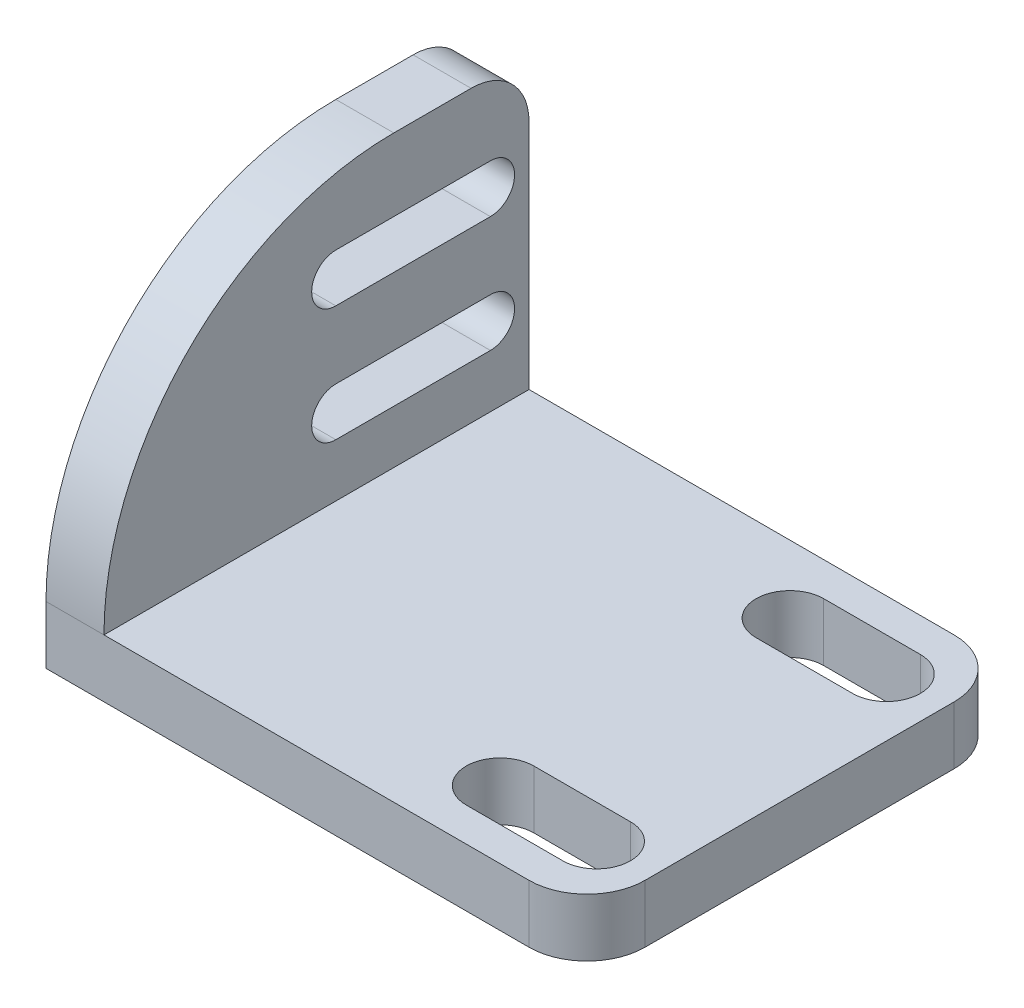
SolidWorks part; units mm, degrees
ref_plane "Front Plane" through (0, 0, 0) normal (0, 0, 1) x (1, 0, 0)
ref_plane "Top Plane" through (0, 0, 0) normal (0, 1, 0) x (1, 0, 0)
ref_plane "Right Plane" through (0, 0, 0) normal (1, 0, 0) x (0, 0, -1)
sketch "Sketch1" plane through (0, 0, 0) normal (0, 0, 1) x (1, 0, 0)
  line L2 (0, 0) -> (0, 15)
  line L3 (0, 15) -> (-3, 15)
  line L4 (-3, -3) -> (-3, 15)
  line L5 (0, 0) -> (25, 0)
  line L7 (-3, -3) -> (25, -3)
  line L8 (25, 0) -> (25, -3)
  dimension "D1" = 15
  dimension "D2" = 25
  dimension "D3" = 3
  dimension "D4" = 3
extrude "Boss-Extrude1" add sketch "Sketch1" along normal blind 22
sketch "Sketch2" plane through (0, 0, 0) normal (0, 1, 0) x (1, 0, 0)
  line L0 (25, -22) -> (25, 0) construction
  line L1 (17, -1.75) -> (22, -1.75)
  line L2 (17, -5.25) -> (22, -5.25)
  line L3 (17, -16.75) -> (22, -16.75)
  line L4 (17, -20.25) -> (22, -20.25)
  arc A0 (22, -5.25) -> (22, -1.75) centre (22, -3.5) ccw
  arc A1 (22, -20.25) -> (22, -16.75) centre (22, -18.5) ccw
  arc A2 (17, -1.75) -> (17, -5.25) centre (17, -3.5) ccw
  arc A3 (17, -16.75) -> (17, -20.25) centre (17, -18.5) ccw
  point P7 (25, -11)
  dimension "D1" = 5
  dimension "D2" = 3.5
  dimension "D3" = 15
  dimension "D4" = 7.5
  dimension "D5" = 3
extrude "Cut-Extrude1" cut sketch "Sketch2" against normal through all
sketch "Sketch3" plane through (0, 0, 0) normal (1, 0, 0) x (0, 0, -1)
  line L1 (-22, 15) -> (0, 15) construction
  line L2 (-22, 0) -> (0, 0) construction
  line L3 (-10, 11.25) -> (-2, 11.25)
  line L4 (-10, 8.75) -> (-2, 8.75)
  line L5 (-10, 5.25) -> (-2, 5.25)
  line L6 (-10, 2.75) -> (-2, 2.75)
  arc A0 (-2, 2.75) -> (-2, 5.25) centre (-2, 4) ccw
  arc A1 (-10, 5.25) -> (-10, 2.75) centre (-10, 4) ccw
  arc A2 (-10, 11.25) -> (-10, 8.75) centre (-10, 10) ccw
  arc A3 (-2, 8.75) -> (-2, 11.25) centre (-2, 10) ccw
  point P8 (-11, 15)
  dimension "D1" = 2.5
  dimension "D2" = 8
  dimension "D3" = 9
  dimension "D4" = 4
  dimension "D5" = 6
extrude "Cut-Extrude2" cut sketch "Sketch3" against normal through all
fillet "Fillet1" radius 15 1 edges at (-1.5, 15, 22)
fillet "Fillet2" radius 3 3 edges at (25, -1.5, 22) (25, -1.5, 0) (-1.5, 15, 0)
